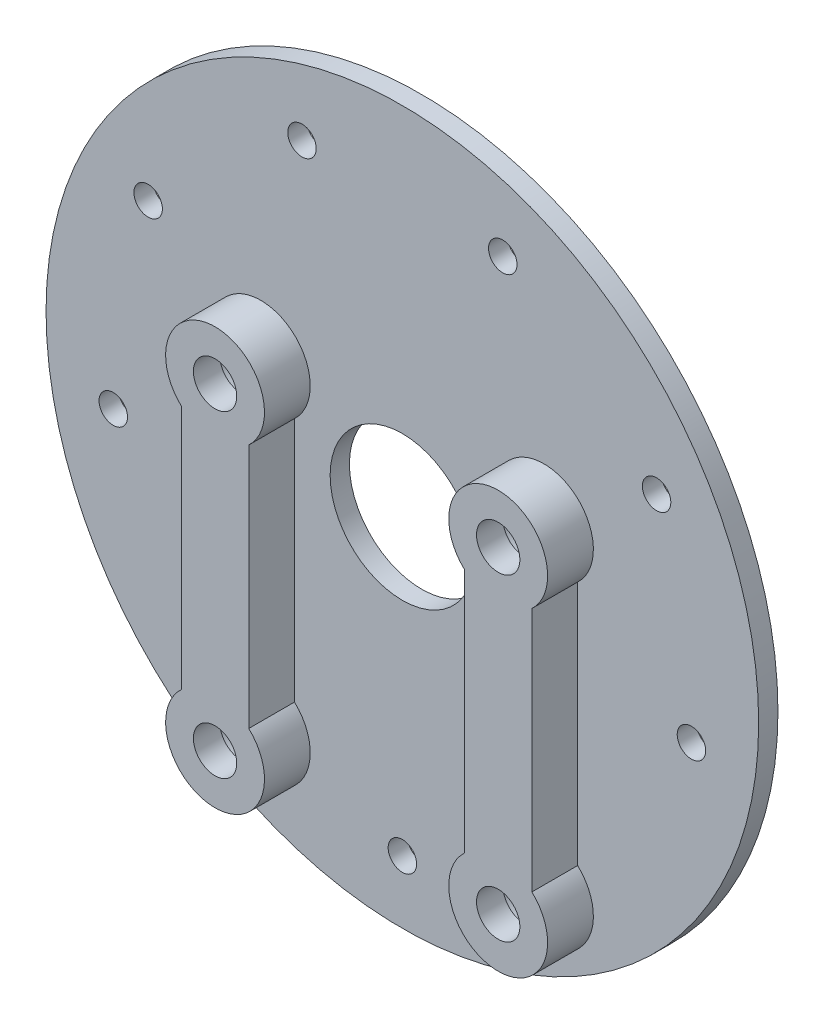
SolidWorks part; units mm, degrees
ref_plane "Ön Düzlem" through (0, 0, 0) normal (0, 0, 1) x (1, 0, 0)
ref_plane "Üst Düzlem" through (0, 0, 0) normal (0, 1, 0) x (1, 0, 0)
ref_plane "Sağ Düzlem" through (0, 0, 0) normal (1, 0, 0) x (0, 0, -1)
sketch "Çizim1" plane through (0, 0, 0) normal (0, 1, 0) x (1, 0, 0)
  line L0 (37, 0) -> (0, 0)
  line L1 (0, 0) -> (0, -2)
  line L2 (0, -2) -> (37, -2)
  line L3 (37, -2) -> (37, 0)
  line L4 (0, 0) -> (0, -2) construction
revolve "Döndür1" add sketch "Çizim1" angle 360 about L4
sketch "Çizim2" plane through (0, 0, 2) normal (0, 0, 1) x (1, 0, 0)
  line L0 (-18.2, -22.2465) -> (-18.2, 3.2464)
  line L1 (-11.2, 3.2464) -> (-11.2, -22.2465)
  arc A0 (-18.2, 3.2464) -> (-11.2, 3.2464) centre (-14.7, 7) cw
  arc A1 (-11.2, -22.2465) -> (-18.2, -22.2465) centre (-14.7, -26) cw
extrude "Yükseklik-Ekstrüzyon1" add sketch "Çizim2" along normal blind 4.75
sketch "Çizim3" plane through (0, 0, 2) normal (0, 0, 1) x (1, 0, 0)
  line L0 (18.2, 3.2464) -> (18.2, -22.2465)
  line L1 (11.2, -22.2465) -> (11.2, 3.2464)
  arc A0 (18.2, -22.2465) -> (11.2, -22.2465) centre (14.7, -26) cw
  arc A1 (11.2, 3.2464) -> (18.2, 3.2464) centre (14.7, 7) cw
extrude "Yükseklik-Ekstrüzyon2" add sketch "Çizim3" along normal blind 4.75
hole_wizard "Delik1" positions "Çizim5" profile "Çizim4" legacy
sketch "Çizim5" plane through (0, 0, 2) normal (0, 0, 1) x (1, 0, 0)
  point P0 (-30.0169, -5.2928)
  point P1 (-26.3965, 15.24)
  point P2 (-10.4248, 28.6418)
  point P3 (10.4248, 28.6418)
  point P4 (26.3965, 15.24)
  point P5 (30.0169, -5.2928)
  point P6 (0, -30.48)
sketch "Çizim4" plane through (-30.0169, -5.2928, 2) normal (1, 0, 0) x (0, -1, 0)
  line L0 (0, 0) -> (0, 2)
  line L1 (0, 2) -> (1.4783, 2)
  line L2 (1.4783, 2) -> (1.4783, 0)
  line L3 (1.4783, 0) -> (0, 0)
  line L4 (0, 110) -> (0, -10) construction
  dimension "Diameter" = 2.9566
  dimension "Depth" = 2
hole_wizard "Ø0.15 (0.15) Diameter Hole1" positions "Çizim7" profile "Çizim6" hole size "Ø0.15" standard "Ansi Metric"
sketch "Çizim7" plane through (0, 0, 0) normal (0, 0, -1) x (-1, 0, 0)
  point P0 (0, 0)
sketch "Çizim6" plane through (0, 0, 0) normal (1, 0, 0) x (0, 1, 0)
  line L0 (0, 0) -> (0, 6.75)
  line L1 (0, 6.75) -> (7.5, 6.75)
  line L2 (7.5, 6.75) -> (7.5, 0)
  line L5 (7.5, 0) -> (0, 0)
  line L11 (0, -6.35) -> (0, 107.95) construction
  dimension "Thru Hole Dia." = 15
  dimension "Thru Hole Depth" = 6.75
hole_wizard "M7x1.0 Tapped Hole1" positions "Çizim9" profile "Çizim8" tap size "M7x1.0" standard "Ansi Metric"
sketch "Çizim9" plane through (0, 0, 0) normal (0, 0, -1) x (-1, 0, 0)
  point P0 (14.7, -26)
  point P1 (-14.7, 7)
  point P2 (-14.7, -26)
  point P3 (14.7, 7)
sketch "Çizim8" plane through (-14.7, -26, 0) normal (1, 0, 0) x (0, 1, 0)
  line L0 (0, 0) -> (0, 6.75)
  line L1 (0, 6.75) -> (2.25, 6.75)
  line L3 (2.25, 6.75) -> (2.25, 4)
  line L4 (2.25, 4) -> (3.5, 4)
  line L5 (3.5, 4) -> (3.5, 0)
  line L7 (3.5, 0) -> (0, 0)
  line L11 (0, -6.35) -> (0, 107.95) construction
  dimension "Thru Tap Drill Dia." = 4.5
  dimension "Thru Tap Drill Depth" = 6.75
  dimension "Thread Major Dia." = 7
  dimension "Thread Depth" = 4
